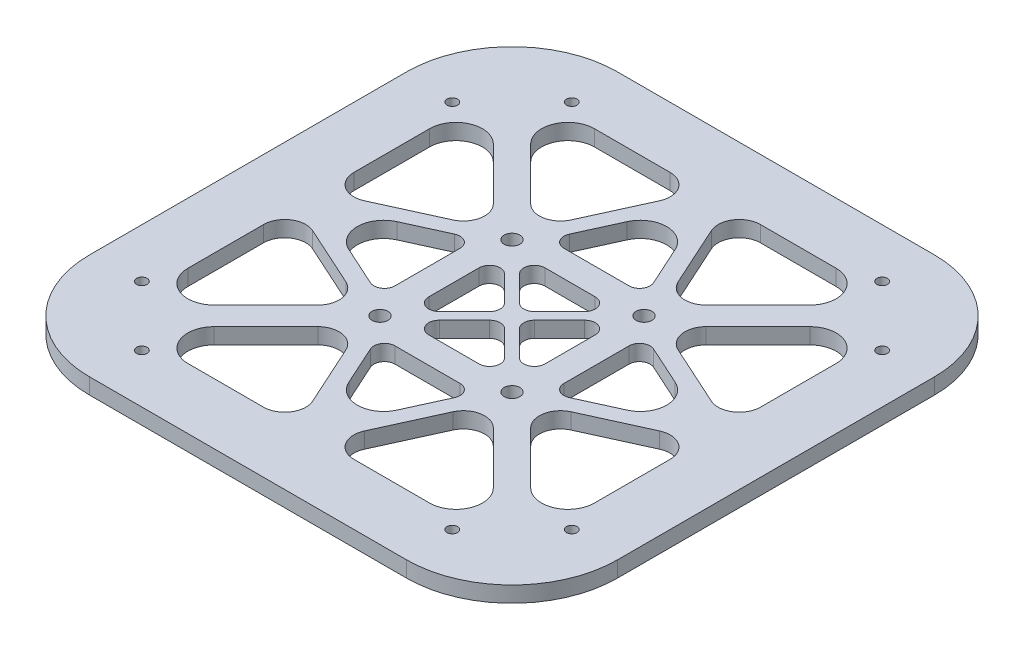
SolidWorks part; units mm, degrees
ref_plane "Plan de face" through (0, 0, 0) normal (0, 0, 1) x (1, 0, 0)
ref_plane "Plan de dessus" through (0, 0, 0) normal (0, 1, 0) x (1, 0, 0)
ref_plane "Plan de droite" through (0, 0, 0) normal (1, 0, 0) x (0, 0, -1)
sketch "Esquisse1" plane through (0, 0, 0) normal (0, 1, 0) x (1, 0, 0)
  line L0 (-50, 50) -> (50, -50) construction
  line L1 (-50, 50) -> (50, 50)
  line L2 (-50, 50) -> (-50, -50)
  line L3 (-50, -50) -> (50, -50)
  line L4 (50, 50) -> (50, -50)
  line L5 (50, 50) -> (-50, -50) construction
  line L6 (-12.5, 12.5) -> (12.5, 12.5) construction
  line L7 (12.5, 12.5) -> (12.5, -12.5) construction
  line L8 (12.5, -12.5) -> (-12.5, -12.5) construction
  line L9 (-12.5, -12.5) -> (-12.5, 12.5) construction
  line L10 (-40, -40) -> (40, -40) construction
  line L11 (40, -40) -> (40, 40) construction
  line L12 (40, 40) -> (-40, 40) construction
  line L13 (-40, 40) -> (-40, -40) construction
  line L14 (-12.5, -12.5) -> (0, -40) construction
  line L15 (0, -40) -> (12.5, -12.5) construction
  line L16 (-9.2614, -16) -> (0, -36.3751)
  line L17 (0, -36.3751) -> (9.2614, -16)
  line L18 (0, -1.4142) -> (-9.5858, -11)
  line L19 (-9.5858, -11) -> (9.5858, -11)
  line L20 (9.5858, -11) -> (0, -1.4142)
  line L21 (9.2614, -16) -> (-9.2614, -16)
  line L22 (-34.9645, -38.5) -> (-2.3295, -38.5)
  line L23 (-2.3295, -38.5) -> (-12.5279, -16.0635)
  line L24 (-12.5279, -16.0635) -> (-34.9645, -38.5)
  line L25 (34.9645, -38.5) -> (2.3295, -38.5)
  line L26 (2.3295, -38.5) -> (12.5279, -16.0635)
  line L27 (12.5279, -16.0635) -> (34.9645, -38.5)
  line L28 (-16, 9.2614) -> (-36.3751, 0)
  line L29 (-36.3751, 0) -> (-16, -9.2614)
  line L30 (-1.4142, 0) -> (-11, 9.5858)
  line L31 (-11, 9.5858) -> (-11, -9.5858)
  line L32 (-11, -9.5858) -> (-1.4142, 0)
  line L33 (-16, -9.2614) -> (-16, 9.2614)
  line L34 (-38.5, 34.9645) -> (-38.5, 2.3295)
  line L35 (-38.5, 2.3295) -> (-16.0635, 12.5279)
  line L36 (-16.0635, 12.5279) -> (-38.5, 34.9645)
  line L37 (-38.5, -34.9645) -> (-38.5, -2.3295)
  line L38 (-38.5, -2.3295) -> (-16.0635, -12.5279)
  line L39 (-16.0635, -12.5279) -> (-38.5, -34.9645)
  line L40 (-12.5, -12.5) -> (-12.5, 12.5) construction
  line L41 (-12.5, 12.5) -> (-40, 0) construction
  line L42 (-40, 0) -> (-12.5, -12.5) construction
  line L43 (9.2614, 16) -> (0, 36.3751)
  line L44 (0, 36.3751) -> (-9.2614, 16)
  line L45 (0, 1.4142) -> (9.5858, 11)
  line L46 (9.5858, 11) -> (-9.5858, 11)
  line L47 (-9.5858, 11) -> (0, 1.4142)
  line L48 (-9.2614, 16) -> (9.2614, 16)
  line L49 (34.9645, 38.5) -> (2.3295, 38.5)
  line L50 (2.3295, 38.5) -> (12.5279, 16.0635)
  line L51 (12.5279, 16.0635) -> (34.9645, 38.5)
  line L52 (-34.9645, 38.5) -> (-2.3295, 38.5)
  line L53 (-2.3295, 38.5) -> (-12.5279, 16.0635)
  line L54 (-12.5279, 16.0635) -> (-34.9645, 38.5)
  line L55 (-12.5, 12.5) -> (12.5, 12.5) construction
  line L56 (12.5, 12.5) -> (0, 40) construction
  line L57 (0, 40) -> (-12.5, 12.5) construction
  line L58 (16, -9.2614) -> (36.3751, 0)
  line L59 (36.3751, 0) -> (16, 9.2614)
  line L60 (1.4142, 0) -> (11, -9.5858)
  line L61 (11, -9.5858) -> (11, 9.5858)
  line L62 (11, 9.5858) -> (1.4142, 0)
  line L63 (16, 9.2614) -> (16, -9.2614)
  line L64 (38.5, -34.9645) -> (38.5, -2.3295)
  line L65 (38.5, -2.3295) -> (16.0635, -12.5279)
  line L66 (16.0635, -12.5279) -> (38.5, -34.9645)
  line L67 (38.5, 34.9645) -> (38.5, 2.3295)
  line L68 (38.5, 2.3295) -> (16.0635, 12.5279)
  line L69 (16.0635, 12.5279) -> (38.5, 34.9645)
  line L70 (12.5, 12.5) -> (12.5, -12.5) construction
  line L71 (12.5, -12.5) -> (40, 0) construction
  line L72 (40, 0) -> (12.5, 12.5) construction
  line L73 (-43.4301, -26.6704) -> (-27.971, -42.1295) construction
  line L74 (-26.6704, 43.4301) -> (-42.1295, 27.971) construction
  line L75 (26.6704, -43.4301) -> (42.1295, -27.971) construction
  line L76 (43.4301, 26.6704) -> (27.971, 42.1295) construction
  circle A0 centre (-12.5, -12.5) radius 1.5
  circle A1 centre (12.5, -12.5) radius 1.5
  circle A2 centre (-12.5, 12.5) radius 1.5
  circle A3 centre (12.5, 12.5) radius 1.5
  circle A4 centre (40.7071, -29.3934) radius 1
  circle A5 centre (29.3934, -40.7071) radius 1
  circle A6 centre (-29.3934, -40.7071) radius 1
  circle A7 centre (-40.7071, -29.3934) radius 1
  circle A8 centre (-40.7071, 29.3934) radius 1
  circle A9 centre (-29.3934, 40.7071) radius 1
  circle A10 centre (29.3934, 40.7071) radius 1
  circle A11 centre (40.7071, 29.3934) radius 1
  dimension "D18" = 8
  dimension "D15" = 7
  dimension "D1" = 1.5
  dimension "D2" = 100
  dimension "D3" = 10
  dimension "D4" = 100
  dimension "D5" = 50
  dimension "D6" = 50
  dimension "D7" = 1
  dimension "D8" = 25
  dimension "D9" = 3.5
  dimension "D10" = 1.5
  dimension "D11" = 1.5
  dimension "D12" = 1.5
  dimension "D13" = 1.5
  dimension "D14" = 2.5
  dimension "D16" = 1.5
  dimension "D17" = 4
  dimension "D19" = 8
  dimension "D20" = 4
extrude "Boss.-Extru.1" add sketch "Esquisse1" along normal blind 3
fillet "Congé1" radius 20 4 edges at (-50, 1.5, -50) (50, 1.5, -50) (50, 1.5, 50) (-50, 1.5, 50)
fillet "Congé2" radius 5 12 edges at (0, 1.5, 36.3751) (36.3751, 1.5, 0) (-36.3751, 1.5, 0) (0, 1.5, -36.3751) (34.9645, 1.5, 38.5) (38.5, 1.5, 34.9645) (38.5, 1.5, -34.9645) (34.9645, 1.5, -38.5) (-34.9645, 1.5, -38.5) (-38.5, 1.5, -34.9645) (-38.5, 1.5, 34.9645) (-34.9645, 1.5, 38.5)
fillet "Congé3" radius 4 16 edges at (2.3295, 1.5, -38.5) (-12.5279, 1.5, -16.0635) (12.5279, 1.5, -16.0635) (38.5, 1.5, -2.3295) (-2.3295, 1.5, 38.5) (16.0635, 1.5, -12.5279) (16.0635, 1.5, 12.5279) (2.3295, 1.5, 38.5) (-2.3295, 1.5, -38.5) (38.5, 1.5, 2.3295) (-16.0635, 1.5, 12.5279) (12.5279, 1.5, 16.0635) (-12.5279, 1.5, 16.0635) (-38.5, 1.5, 2.3295) (-16.0635, 1.5, -12.5279) (-38.5, 1.5, -2.3295)
fillet "Congé4" radius 2 20 edges at (16, 1.5, 9.2614) (9.5858, 1.5, 11) (-9.5858, 1.5, 11) (-9.2614, 1.5, -16) (9.2614, 1.5, -16) (11, 1.5, 9.5858) (9.5858, 1.5, -11) (11, 1.5, -9.5858) (9.2614, 1.5, 16) (1.4142, 1.5, 0) (-9.5858, 1.5, -11) (16, 1.5, -9.2614) (-9.2614, 1.5, 16) (0, 1.5, 1.4142) (-11, 1.5, 9.5858) (-1.4142, 1.5, 0) (-11, 1.5, -9.5858) (-16, 1.5, 9.2614) (-16, 1.5, -9.2614) (0, 1.5, -1.4142)
